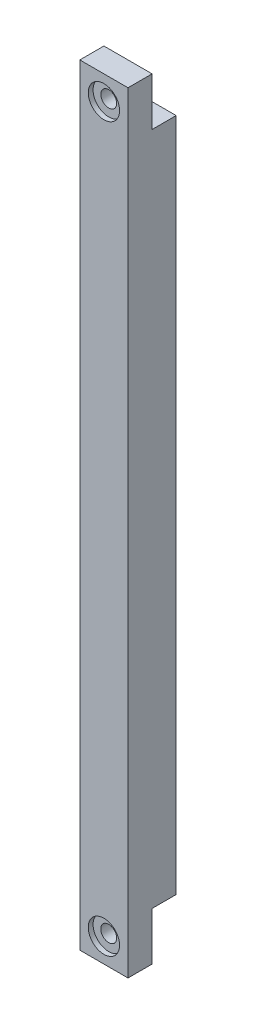
SolidWorks part; units mm, degrees
ref_plane "前视基准面" through (0, 0, 0) normal (0, 0, 1) x (1, 0, 0)
ref_plane "上视基准面" through (0, 0, 0) normal (0, 1, 0) x (1, 0, 0)
ref_plane "右视基准面" through (0, 0, 0) normal (1, 0, 0) x (0, 0, -1)
other "Configuration Table"
sketch "草图1" plane through (0, 0, 0) normal (0, 0, 1) x (1, 0, 0)
  line L1 (0, 0) -> (10, 0)
  line L2 (0, 0) -> (0, -160)
  line L3 (0, -160) -> (10, -160)
  line L4 (10, 0) -> (10, -160)
  line L5 (0, 0) -> (10, -160) construction
  line L6 (0, -160) -> (10, 0) construction
  point P4 (5, -80)
  dimension "D1" = 10
  dimension "D2" = 160
extrude "凸台-拉伸1" add sketch "草图1" along normal blind 10
sketch "草图3" plane through (0, 0, 0) normal (0, 0, -1) x (-1, 0, 0)
  line L0 (0, 0) -> (0, -160) construction
  line L1 (-10, 0) -> (0, 0)
  line L2 (-10, 0) -> (-10, -10)
  line L3 (-10, -10) -> (0, -10)
  line L4 (0, 0) -> (0, -10)
  line L5 (-10, 0) -> (0, -10) construction
  line L6 (-10, -10) -> (0, 0) construction
  line L8 (-10, -160) -> (0, -160)
  line L9 (-10, -160) -> (-10, -150)
  line L10 (-10, -150) -> (0, -150)
  line L11 (0, -160) -> (0, -150)
  line L12 (-10, -160) -> (0, -150) construction
  line L13 (-10, -150) -> (0, -160) construction
  point P4 (-5, -5)
  point P12 (-5, -155)
  dimension "D1" = 10
  dimension "D2" = 10
extrude "切除-拉伸1" cut sketch "草图3" against normal blind 5
sketch "草图7" plane through (0, 0, 10) normal (0, 0, 1) x (1, 0, 0)
  line L0 (10, -160) -> (10, 0) construction
  line L1 (0, 0) -> (10, 0) construction
  line L2 (0, 0) -> (0, -10) construction
  line L3 (0, -10) -> (10, -10) construction
  line L4 (10, 0) -> (10, -10) construction
  line L5 (0, 0) -> (10, -10) construction
  line L6 (0, -10) -> (10, 0) construction
  line L8 (0, -160) -> (10, -160) construction
  line L9 (0, -160) -> (0, -150) construction
  line L10 (0, -150) -> (10, -150) construction
  line L11 (10, -160) -> (10, -150) construction
  line L12 (0, -160) -> (10, -150) construction
  line L13 (0, -150) -> (10, -160) construction
  circle A0 centre (5, -5) radius 3.25
  circle A1 centre (5, -155) radius 3.25
  point P4 (5, -5)
  point P12 (5, -155)
  dimension "D3" = 6.5
  dimension "D4" = 6.5
  dimension "D1" = 10
  dimension "D2" = 10
hole_wizard "M4 螺纹孔的螺纹孔钻头1" positions "草图8" profile "草图9" hole size "M4" standard "ISO" end condition through all
sketch "草图8" plane through (0, 0, 10) normal (0, 0, 1) x (1, 0, 0)
  point P0 (5, -5)
  point P3 (5, -155)
sketch "草图9" plane through (5, -5, 10) normal (1, 0, 0) x (0, -1, 0)
  line L0 (0, 0) -> (0, 10)
  line L1 (0, 10) -> (1.65, 10)
  line L2 (1.65, 10) -> (1.65, 0)
  line L5 (1.65, 0) -> (0, 0)
  line L11 (0, -6.35) -> (0, 107.95) construction
  dimension "通孔孔直径" = 3.3
  dimension "通孔孔深度" = 10
extrude "切除-拉伸2" cut sketch "草图7" against normal blind 1
